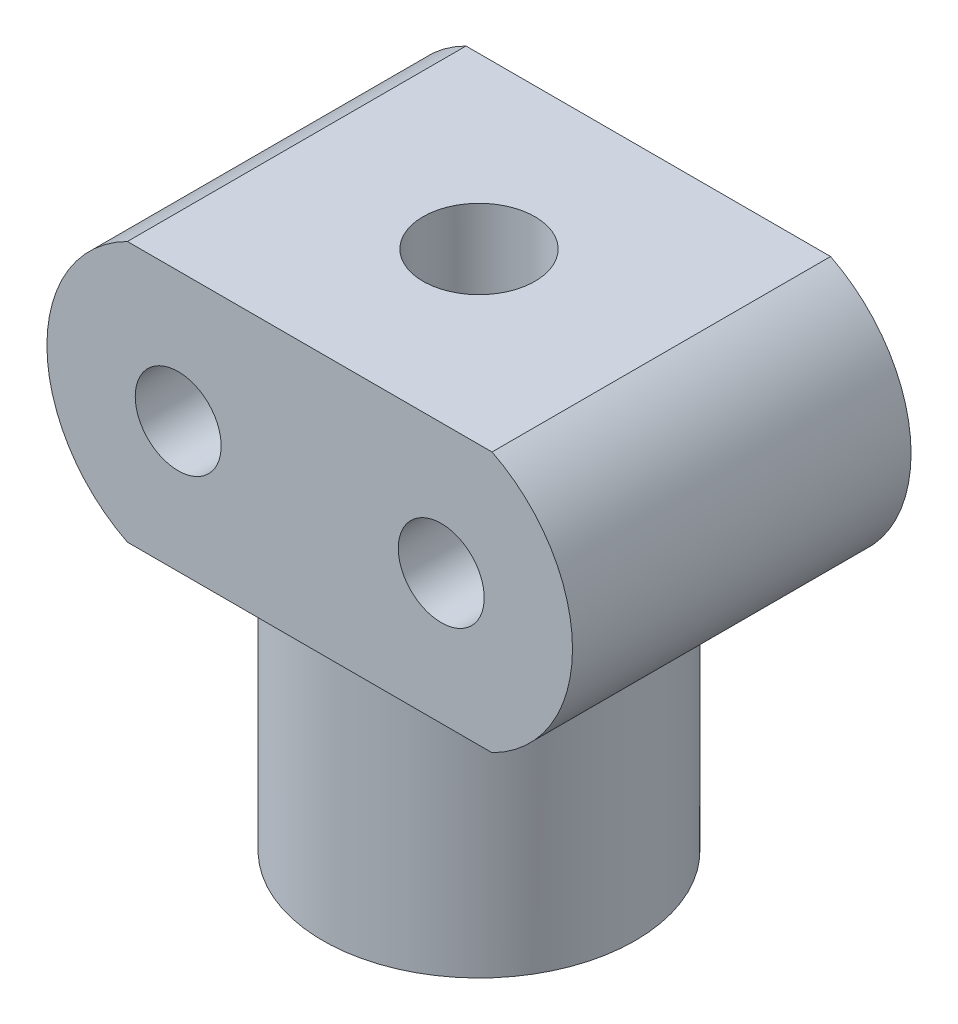
SolidWorks part; units mm, degrees
ref_plane "Front Plane" through (0, 0, 0) normal (0, 0, 1) x (1, 0, 0)
ref_plane "Top Plane" through (0, 0, 0) normal (0, 1, 0) x (1, 0, 0)
ref_plane "Right Plane" through (0, 0, 0) normal (1, 0, 0) x (0, 0, -1)
sketch "Sketch2" plane through (0, 0, 0) normal (0, 0, 1) x (1, 0, 0)
  line L1 (7, -5) -> (-7, -5)
  line L3 (7, 5) -> (-7, 5)
  line L5 (7, -5) -> (-7, 5) construction
  line L6 (7, 5) -> (-7, -5) construction
  arc A0 (7, 5) -> (7, -5) centre (4.5, 0) cw
  arc A1 (-7, 5) -> (-7, -5) centre (-4.5, 0) ccw
  point P0 (0, 0)
  dimension "D3" = 4.5
  dimension "D1" = 10
  dimension "D2" = 14
  dimension "D4" = 14
  dimension "D5" = 4.5
  dimension "D6" = 10
extrude "Boss-Extrude1" add sketch "Sketch2" along normal blind 13
sketch "Sketch4" plane through (0, 5, 0) normal (0, 1, 0) x (1, 0, 0)
  circle A0 centre (0, -6.5) radius 2.15
  dimension "D1" = 4.3
sketch "Sketch8" plane through (0, 0, 0) normal (0, 0, -1) x (-1, 0, 0)
  circle A0 centre (-5.05, 0) radius 1.65
  circle A1 centre (5.05, 0) radius 1.65
  dimension "D1" = 3.3
  dimension "D2" = 3.3
  dimension "D3" = 5.05
  dimension "D4" = 5.05
extrude "Cut-Extrude4" cut sketch "Sketch8" against normal through all
sketch "Sketch6" plane through (0, -5, 0) normal (0, -1, 0) x (1, 0, 0)
  circle A0 centre (0, 6.5) radius 6
  dimension "D1" = 12
extrude "Boss-Extrude2" add sketch "Sketch6" along normal blind 10
extrude "Cut-Extrude3" cut sketch "Sketch4" against normal up to surface (20 mm away) up to face at (6, -15, 6.5)
equation "\"D3@Sketch2\"=\"D5@Sketch2\""
equation "\"D6@Sketch2\" =\"D1@Sketch2\""
equation "\"D4@Sketch2\"=\"D2@Sketch2\""
equation "\"D1@Sketch8\"=\"D2@Sketch8\""
equation "\"D4@Sketch8\" = \"D3@Sketch8\""
